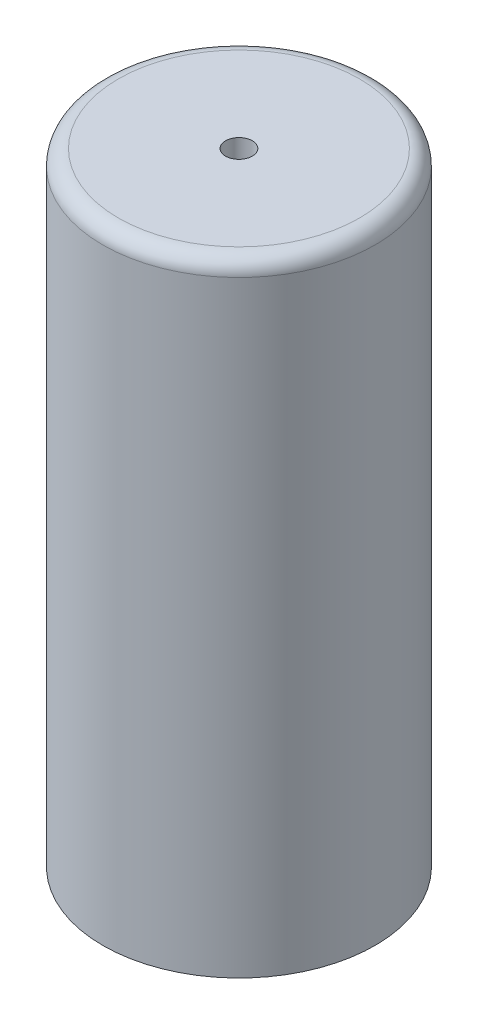
SolidWorks part; units mm, degrees
ref_plane "Front Plane" through (0, 0, 0) normal (0, 0, 1) x (1, 0, 0)
ref_plane "Top Plane" through (0, 0, 0) normal (0, 1, 0) x (1, 0, 0)
ref_plane "Right Plane" through (0, 0, 0) normal (1, 0, 0) x (0, 0, -1)
sketch "Sketch1" plane through (0, 0, 0) normal (0, 1, 0) x (1, 0, 0)
  circle A0 centre (0, 0) radius 22.225
  dimension "D1" = 44.45
extrude "Boss-Extrude1" add sketch "Sketch1" along normal blind 101.6
fillet "Fillet1" radius 2.54 1 edges at (0, 101.6, 22.225)
sketch "Sketch2" plane through (0, 101.6, 0) normal (0, 1, 0) x (1, 0, 0)
  circle A0 centre (0, 0) radius 2.1828
  dimension "D1" = 4.3656
extrude "Cut-Extrude1" cut sketch "Sketch2" against normal blind 6.858
